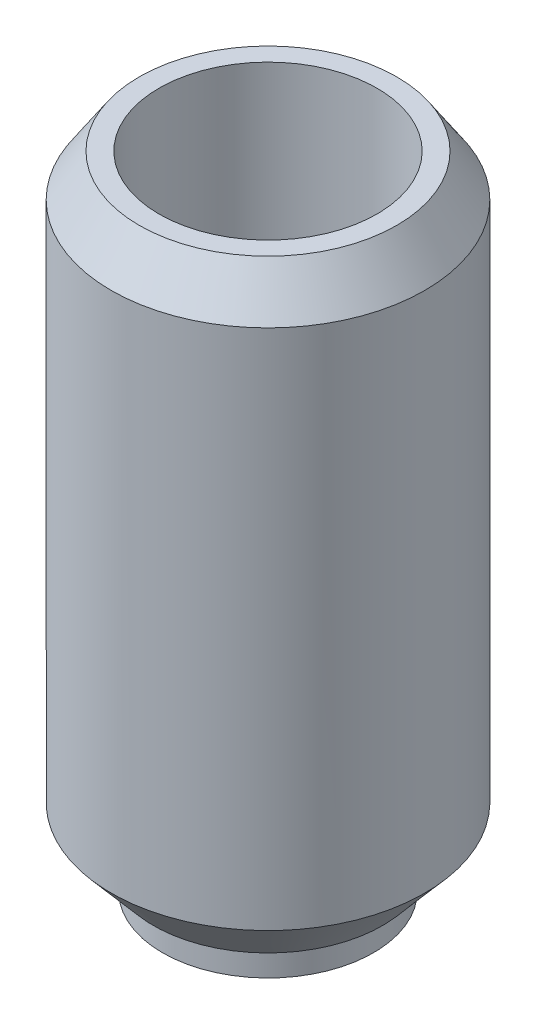
SolidWorks part; units mm, degrees
material "1.4031(X39Cr13)"
ref_plane "Plan de face" through (0, 0, 0) normal (0, 0, 1) x (1, 0, 0)
ref_plane "Plan de dessus" through (0, 0, 0) normal (0, 1, 0) x (1, 0, 0)
ref_plane "Plan de droite" through (0, 0, 0) normal (1, 0, 0) x (0, 0, -1)
other "Centre de masse"
sketch "Esquisse1" plane through (0, 0, 0) normal (0, 1, 0) x (1, 0, 0)
  circle A0 centre (0, 0) radius 11.15
  dimension "D1" = 22.3
extrude "Boss.-Extru.1" add sketch "Esquisse1" along normal blind 45.6
sketch "Esquisse2" plane through (0, 45.6, 0) normal (0, 1, 0) x (1, 0, 0)
  circle A0 centre (0, 0) radius 7.75
  dimension "D1" = 15.5
extrude "Enlèv. mat.-Extru.1" cut sketch "Esquisse2" against normal blind 33
sketch "Esquisse3" plane through (0, 0, 0) normal (0, -1, 0) x (1, 0, 0)
  circle A0 centre (0, 0) radius 7.5
  circle A1 centre (0, 0) radius 11.15
  dimension "D1" = 15
extrude "Enlèv. mat.-Extru.2" cut sketch "Esquisse3" against normal blind 2
sketch "Esquisse4" plane through (0, 0, 0) normal (0, -1, 0) x (1, 0, 0)
  circle A0 centre (0, 0) radius 3.75
  dimension "D1" = 7.5
extrude "Enlèv. mat.-Extru.3" cut sketch "Esquisse4" against normal through all
chamfer "Chanfrein1" distance 3 distance2 2 1 edges at (0, 45.6, 11.15)
chamfer "Chanfrein2" distance 3.5 distance2 3 1 edges at (0, 2, -11.15)
